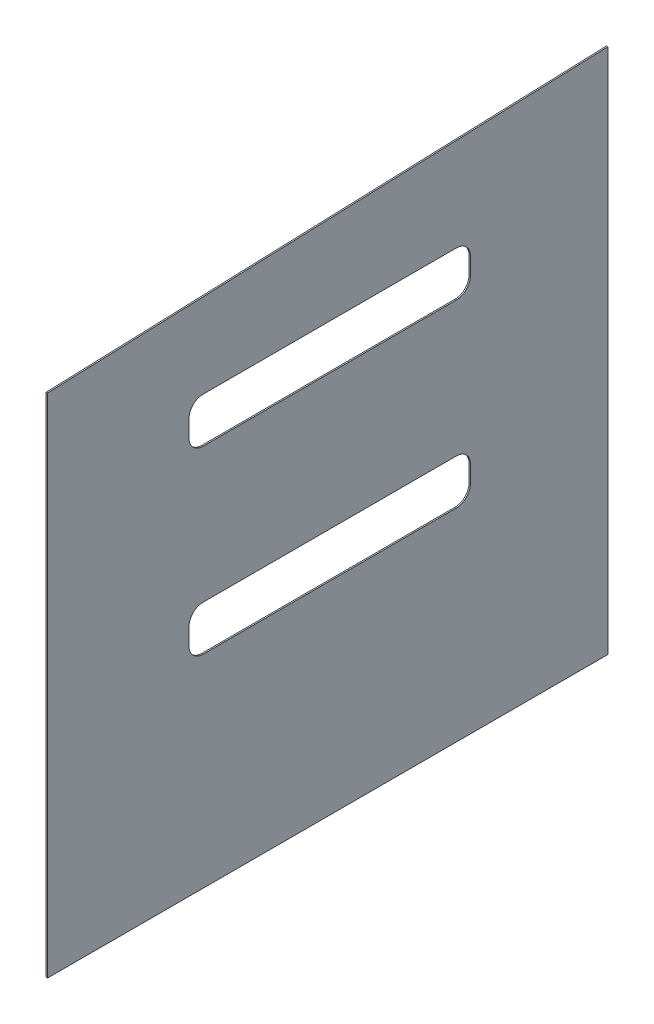
SolidWorks part; units mm, degrees
material "S-Glass Fiber"
ref_plane "Front Plane" through (0, 0, 0) normal (0, 0, 1) x (1, 0, 0)
ref_plane "Top Plane" through (0, 0, 0) normal (0, 1, 0) x (1, 0, 0)
ref_plane "Right Plane" through (0, 0, 0) normal (1, 0, 0) x (0, 0, -1)
sketch "Sketch1" plane through (0, 0, 0) normal (1, 0, 0) x (0, 0, -1)
  line L0 (-746.3982, -447.5427) -> (1780.9018, -447.5427)
  line L1 (1780.9018, -447.5427) -> (1780.9018, 1927.3573)
  line L2 (1780.9018, 1927.3573) -> (-746.3982, 1838.4573)
  line L3 (-746.3982, 1838.4573) -> (-746.3982, -447.5427)
  dimension "D1" = 2527.3
  dimension "D2" = 2374.9
  dimension "D3" = 2286
extrude "Boss-Extrude1" add sketch "Sketch1" along normal blind 6.35
sketch "Sketch2" plane through (6.35, 0, 0) normal (1, 0, 0) x (0, 0, -1)
  line L0 (-746.3982, -447.5427) -> (1780.9018, -447.5427) construction
  line L1 (-45.1003, 670.0573) -> (1097.8997, 670.0573)
  line L2 (-108.6003, 606.5573) -> (-108.6003, 530.3573)
  line L3 (-45.1003, 466.8573) -> (1097.8997, 466.8573)
  line L4 (1161.3997, 606.5573) -> (1161.3997, 530.3573)
  line L5 (-108.6003, 670.0573) -> (1161.3997, 466.8573) construction
  line L6 (-108.6003, 466.8573) -> (1161.3997, 670.0573) construction
  line L8 (1097.8997, 1482.8573) -> (-45.1003, 1482.8573)
  line L9 (1161.3997, 1419.3573) -> (1161.3997, 1343.1573)
  line L10 (1097.8997, 1279.6573) -> (-45.1003, 1279.6573)
  line L11 (-108.6003, 1419.3573) -> (-108.6003, 1343.1573)
  line L12 (1161.3997, 1482.8573) -> (-108.6003, 1279.6573) construction
  line L13 (1161.3997, 1279.6573) -> (-108.6003, 1482.8573) construction
  arc A0 (-45.1003, 670.0573) -> (-108.6003, 606.5573) centre (-45.1003, 606.5573) ccw
  arc A1 (-108.6003, 530.3573) -> (-45.1003, 466.8573) centre (-45.1003, 530.3573) ccw
  arc A2 (1097.8997, 466.8573) -> (1161.3997, 530.3573) centre (1097.8997, 530.3573) ccw
  arc A3 (1097.8997, 670.0573) -> (1161.3997, 606.5573) centre (1097.8997, 606.5573) cw
  arc A4 (1161.3997, 1343.1573) -> (1097.8997, 1279.6573) centre (1097.8997, 1343.1573) cw
  arc A5 (1097.8997, 1482.8573) -> (1161.3997, 1419.3573) centre (1097.8997, 1419.3573) cw
  arc A6 (-45.1003, 1279.6573) -> (-108.6003, 1343.1573) centre (-45.1003, 1343.1573) cw
  arc A7 (-45.1003, 1482.8573) -> (-108.6003, 1419.3573) centre (-45.1003, 1419.3573) ccw
  point P0 (526.3997, 568.4573)
  point P7 (526.3997, 1381.2573)
  dimension "D7" = 63.5
  dimension "D1" = 1270
  dimension "D2" = 914.4
  dimension "D3" = 203.2
  dimension "D4" = 1270
  dimension "D5" = 203.2
  dimension "D6" = 609.6
extrude "Cut-Extrude1" cut sketch "Sketch2" against normal blind 50.8
